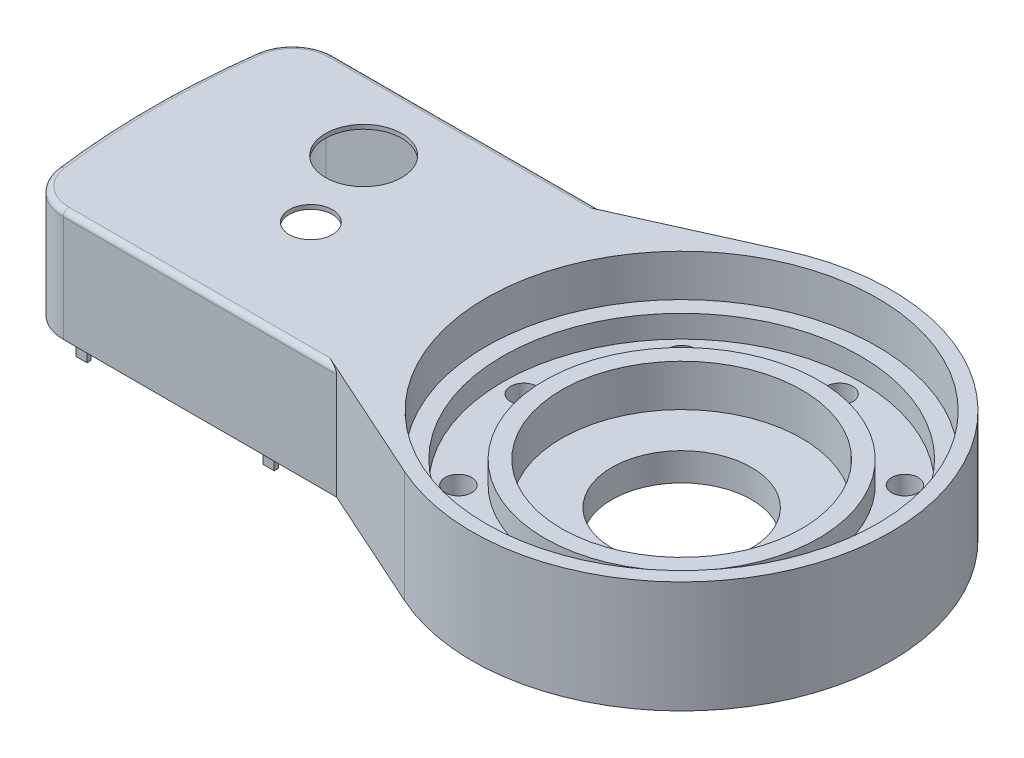
SolidWorks part; units mm, degrees
material "Gray Cast Iron"
ref_plane "Front Plane" through (0, 0, 0) normal (0, 0, 1) x (1, 0, 0)
ref_plane "Top Plane" through (0, 0, 0) normal (0, 1, 0) x (1, 0, 0)
ref_plane "Right Plane" through (0, 0, 0) normal (1, 0, 0) x (0, 0, -1)
sketch "Sketch1" plane through (0, 0, 0) normal (0, 1, 0) x (1, 0, 0)
  line L0 (-257.8328, 48.5) -> (-160, 48.5)
  line L1 (-257.8328, -48.5) -> (-160, -48.5)
  line L2 (-160, -48.5) -> (-115.7695, -68.3976)
  line L3 (-160, 48.5) -> (-115.7695, 68.3976)
  arc A0 (-272.7078, 35.4327) -> (-272.7078, -35.4327) centre (0, 0) ccw
  arc A1 (-257.8328, 48.5) -> (-272.7078, 35.4327) centre (-257.8328, 33.5) ccw
  arc A2 (-272.7078, -35.4327) -> (-257.8328, -48.5) centre (-257.8328, -33.5) ccw
  arc A3 (-115.7695, -68.3976) -> (-115.7695, 68.3976) centre (-85, 0) ccw
  point P1 (-275, 0)
  dimension "D1" = 550
  dimension "D4" = 30
  dimension "D5" = 30
  dimension "D6" = 115
  dimension "D8" = 150
  dimension "D2" = 48.5
  dimension "D3" = 48.5
  dimension "D7" = 75
  dimension "D9" = 48.5
extrude "Boss-Extrude1" add sketch "Sketch1" along normal blind 40
sketch "Sketch2" plane through (0, 40, 0) normal (0, 1, 0) x (1, 0, 0)
  circle A0 centre (-85, 0) radius 70
  dimension "D1" = 140
extrude "Cut-Extrude1" cut sketch "Sketch2" against normal blind 15
sketch "Sketch3" plane through (0, 25, 0) normal (0, 1, 0) x (1, 0, 0)
  circle A0 centre (-85, 0) radius 64
  circle A1 centre (-85, 0) radius 49
  dimension "D1" = 128
  dimension "D2" = 98
extrude "Cut-Extrude3" cut sketch "Sketch3" against normal blind 8
sketch "Sketch4" plane through (0, 17, 0) normal (0, 1, 0) x (1, 0, 0)
  circle A1 centre (-45.0485, -39.9515) radius 4.75
  circle A2 centre (-85, -56.5) radius 4.75
  circle A3 centre (-28.5, 0) radius 4.75
  circle A4 centre (-85, 0) radius 49 construction
  circle A5 centre (-124.9515, -39.9515) radius 4.75
  circle A6 centre (-141.5, 0) radius 4.75
  circle A7 centre (-124.9515, 39.9515) radius 4.75
  circle A8 centre (-85, 56.5) radius 4.75
  circle A9 centre (-45.0485, 39.9515) radius 4.75
  point P4 (-85, 0)
  point P23 (-85, 0)
  dimension "D1" = 9.5
  dimension "D2" = 56.5
  dimension "D3" = 8
extrude "Cut-Extrude4" cut sketch "Sketch4" against normal through all
sketch "Sketch5" plane through (0, 25, 0) normal (0, 1, 0) x (1, 0, 0)
  circle A0 centre (-85, 0) radius 25
  dimension "D1" = 50
extrude "Cut-Extrude5" cut sketch "Sketch5" against normal through all
sketch "Sketch7" plane through (0, 25, 0) normal (0, 1, 0) x (1, 0, 0)
  circle A0 centre (-85, 0) radius 43
  dimension "D1" = 86
extrude "Cut-Extrude6" cut sketch "Sketch7" against normal blind 15
sketch "Sketch8" plane through (0, 0, 0) normal (0, -1, 0) x (1, 0, 0)
  line L0 (-257.8328, 45.5) -> (-160, 45.5)
  line L1 (-257.8328, 48.5) -> (-160, 48.5) construction
  line L2 (-257.8328, -45.5) -> (-160, -45.5)
  line L3 (-160, -48.5) -> (-257.8328, -48.5) construction
  line L4 (-160, 45.5) -> (-160, -45.5)
  arc A0 (-269.7328, 35.0462) -> (-269.7328, -35.0462) centre (0, 0) ccw
  arc A2 (-257.8328, 45.5) -> (-269.7328, 35.0462) centre (-257.8328, 33.5) ccw
  arc A3 (-269.7328, -35.0462) -> (-257.8328, -45.5) centre (-257.8328, -33.5) ccw
  dimension "D2" = 544
  dimension "D3" = 3
  dimension "D1" = 3
extrude "Cut-Extrude7" cut sketch "Sketch8" against normal offset from surface (38.5 mm away) 1.5 up to face at (-85, 40, 70)
sketch "Sketch9" plane through (0, 40, 0) normal (0, 1, 0) x (1, 0, 0)
  circle A0 centre (-221.0596, 22.2364) radius 13.6648
  circle A1 centre (-209.8748, -7.856) radius 7.7228
extrude "Cut-Extrude8" cut sketch "Sketch9" against normal through all
fillet "Fillet1" radius 2 5 edges at (-208.9164, 40, -48.5) (-267.7325, 40, -44.7692) (-208.9164, 40, 48.5) (-267.7325, 40, 44.7692) (-275, 40, 0)
sketch "Sketch10" plane through (0, 0, -45.5) normal (0, 0, 1) x (1, 0, 0)
  line L0 (-257.8328, 0) -> (-160, 0) construction
  line L1 (-254.8328, -4.5) -> (-250.8328, -4.5)
  line L2 (-254.8328, -4.5) -> (-254.8328, 4.5)
  line L3 (-254.8328, 4.5) -> (-250.8328, 4.5)
  line L4 (-250.8328, -4.5) -> (-250.8328, 4.5)
  line L5 (-254.8328, -4.5) -> (-250.8328, 4.5) construction
  line L6 (-254.8328, 4.5) -> (-250.8328, -4.5) construction
  line L8 (-187.8328, -4.5) -> (-183.8328, -4.5)
  line L9 (-187.8328, -4.5) -> (-187.8328, 4.5)
  line L10 (-187.8328, 4.5) -> (-183.8328, 4.5)
  line L11 (-183.8328, -4.5) -> (-183.8328, 4.5)
  line L12 (-187.8328, -4.5) -> (-183.8328, 4.5) construction
  line L13 (-187.8328, 4.5) -> (-183.8328, -4.5) construction
  line L14 (-257.8328, 38) -> (-257.8328, 0) construction
  point P0 (-252.8328, 0)
  point P7 (-185.8328, 0)
  dimension "D1" = 4
  dimension "D2" = 4
  dimension "D3" = 9
  dimension "D4" = 9
  dimension "D5" = 63
  dimension "D6" = 3
extrude "Boss-Extrude2" add sketch "Sketch10" against normal blind 1.5
ref_plane "Plane2" through (0, 0, 0) normal (0, 0, 1) x (1, 0, 0)
mirror "Mirror1" about plane through (0, 0, 0) normal (0, 0, 1) of "Boss-Extrude2"
sketch "Sketch11" plane through (0, 0, 0) normal (0, -1, 0) x (1, 0, 0)
  line L1 (-106, -21) -> (-64, -21) construction
  line L2 (-106, -21) -> (-106, 21) construction
  line L3 (-106, 21) -> (-64, 21) construction
  line L4 (-64, -21) -> (-64, 21) construction
  line L5 (-106, -21) -> (-64, 21) construction
  line L6 (-106, 21) -> (-64, -21) construction
  circle A0 centre (-106, 21) radius 2
  circle A1 centre (-64, 21) radius 2
  circle A2 centre (-64, -21) radius 2
  circle A3 centre (-106, -21) radius 2
  point P0 (-85, 0)
  dimension "D3" = 4
  dimension "D4" = 4
  dimension "D5" = 4
  dimension "D6" = 4
  dimension "D1" = 42
  dimension "D2" = 42
extrude "Cut-Extrude9" cut sketch "Sketch11" against normal blind 4
